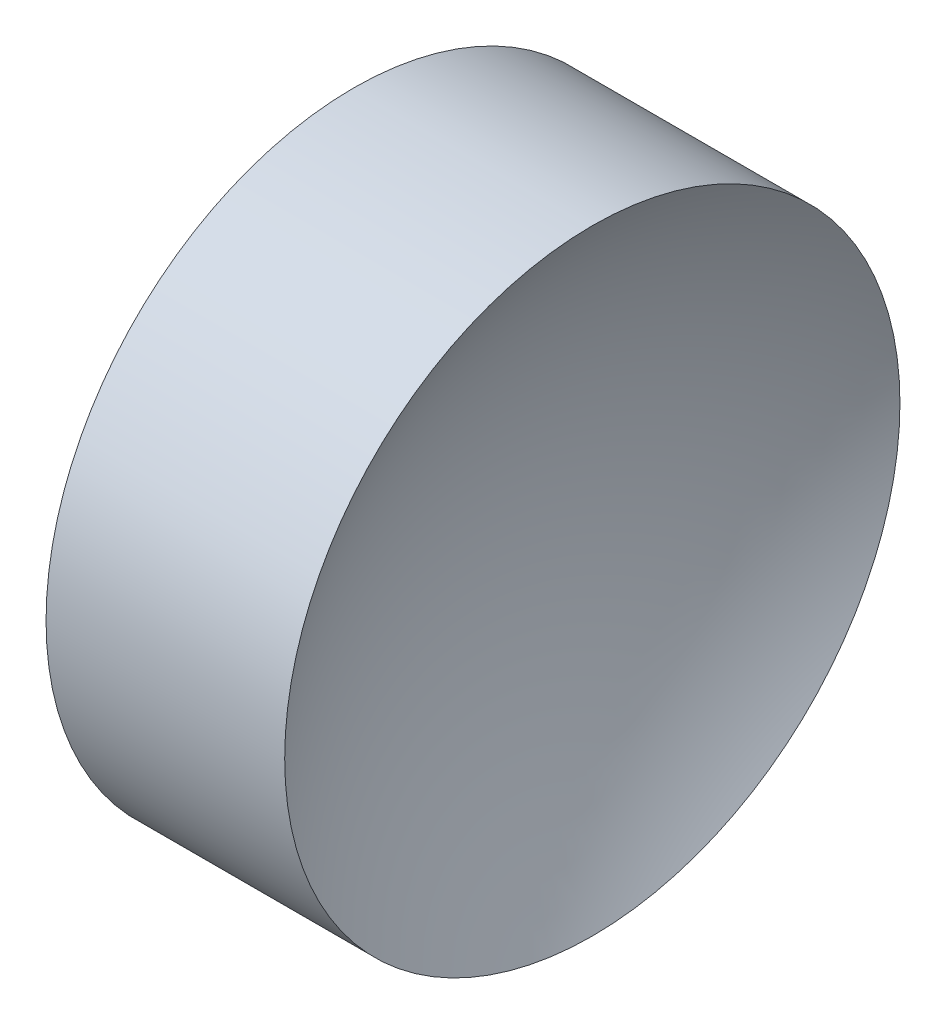
SolidWorks part; units mm, degrees
ref_plane "前视基准面" through (0, 0, 0) normal (0, 0, 1) x (1, 0, 0)
ref_plane "上视基准面" through (0, 0, 0) normal (0, 1, 0) x (1, 0, 0)
ref_plane "右视基准面" through (0, 0, 0) normal (1, 0, 0) x (0, 0, -1)
sketch "草图1" plane through (0, 0, 0) normal (0, 0, 1) x (1, 0, 0)
  line L0 (21.1565, 13.0311) -> (26.8361, 13.0311) construction
  line L1 (22.2009, 13.0311) -> (22.2009, 16.1811)
  line L2 (22.2009, 16.1811) -> (24.6444, 16.1811)
  line L3 (23.7009, 13.0311) -> (22.2009, 13.0311)
  arc A0 (24.6444, 16.1811) -> (23.7009, 13.0311) centre (29.4309, 13.0311) ccw
  dimension "D3" = 5.73
  dimension "D1" = 3.15
  dimension "D2" = 2.4435
revolve "旋转1" add sketch "草图1" angle 360 about L0
